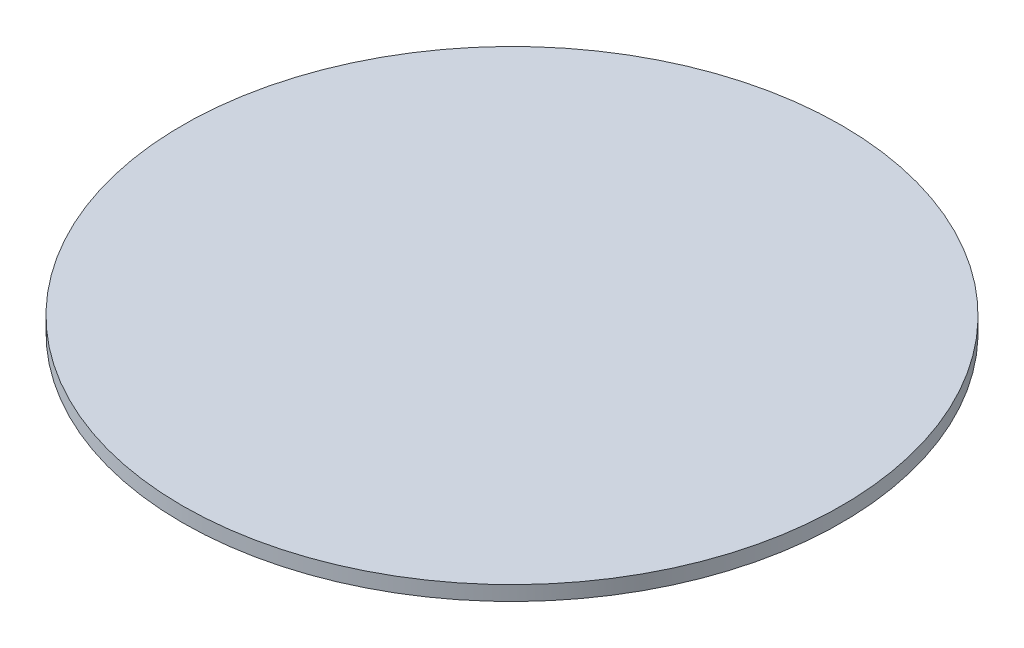
SolidWorks part; units mm, degrees
ref_plane "Front Plane" through (0, 0, 0) normal (0, 0, 1) x (1, 0, 0)
ref_plane "Top Plane" through (0, 0, 0) normal (0, 1, 0) x (1, 0, 0)
ref_plane "Right Plane" through (0, 0, 0) normal (1, 0, 0) x (0, 0, -1)
sketch "Sketch1" plane through (0, 0, 0) normal (0, 1, 0) x (1, 0, 0)
  circle A0 centre (0, 0) radius 45
  dimension "D1" = 90
extrude "Boss-Extrude1" add sketch "Sketch1" along normal blind 2
